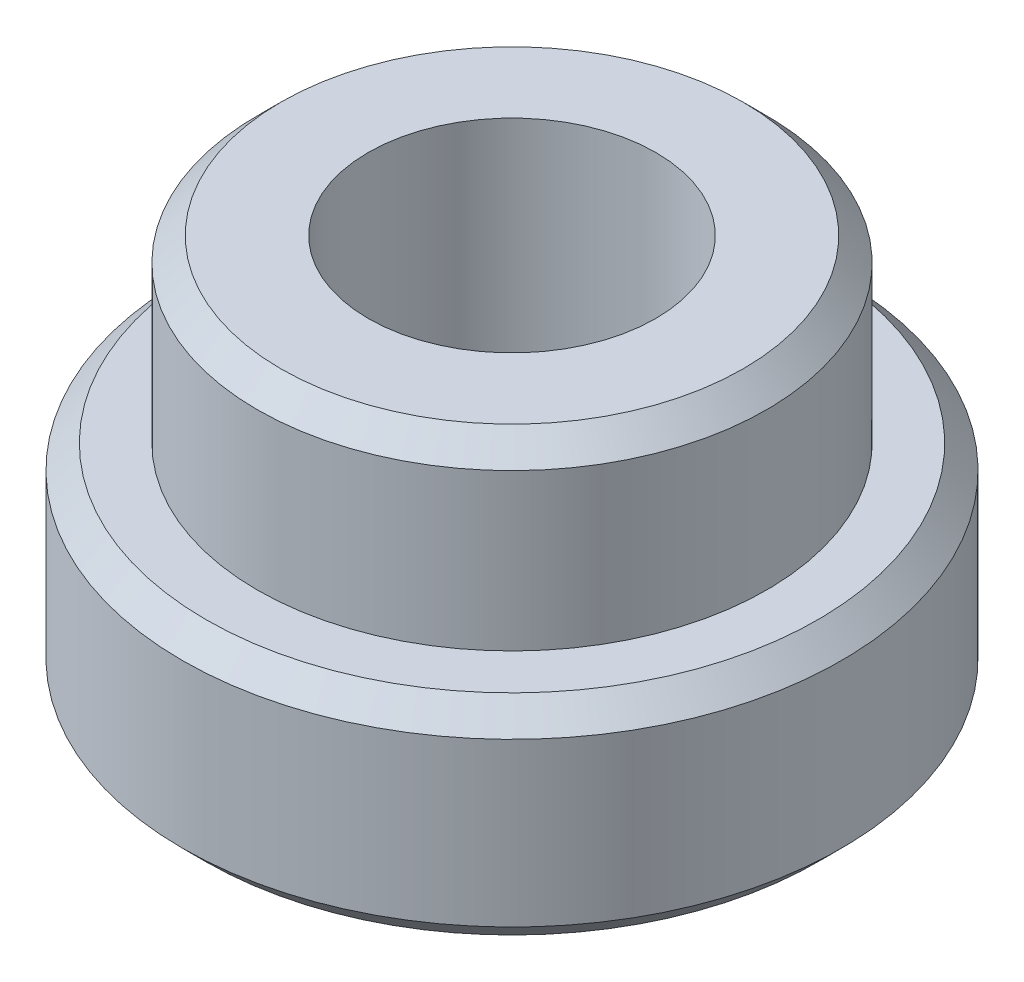
SolidWorks part; units mm, degrees
material "Stainless Steel (ferritic)"
ref_plane "Front Plane" through (0, 0, 0) normal (0, 0, 1) x (1, 0, 0)
ref_plane "Top Plane" through (0, 0, 0) normal (0, 1, 0) x (1, 0, 0)
ref_plane "Right Plane" through (0, 0, 0) normal (1, 0, 0) x (0, 0, -1)
sketch "Sketch1" plane through (0, 0, 0) normal (0, 1, 0) x (1, 0, 0)
  circle A0 centre (0, 0) radius 2.794
  dimension "D1" = 5.588
extrude "Boss-Extrude1" add sketch "Sketch1" along normal blind 1.778
chamfer "Chamfer1" distance 0.2 angle 45 2 edges at (0, 1.778, 2.794) (0, 0, 2.794)
sketch "Sketch2" plane through (0, 1.778, 0) normal (0, 1, 0) x (1, 0, 0)
  circle A0 centre (0, 0) radius 2.159
  dimension "D1" = 4.318
extrude "Boss-Extrude2" add sketch "Sketch2" along normal blind 1.524
chamfer "Chamfer2" distance 0.2 angle 45 1 edges at (0, 3.302, 2.159)
sketch "Sketch3" plane through (0, 3.302, 0) normal (0, 1, 0) x (1, 0, 0)
  circle A0 centre (0, 0) radius 1.2192
  dimension "D1" = 2.4384
extrude "Cut-Extrude1" cut sketch "Sketch3" against normal through all
